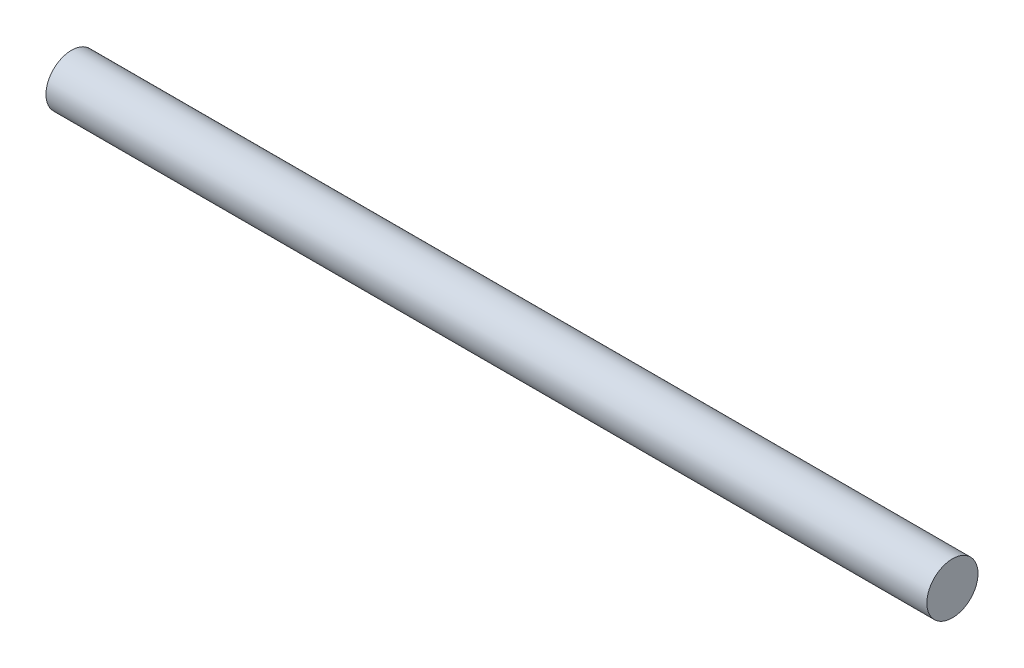
SolidWorks part; units mm, degrees
ref_plane "Plan de face" through (0, 0, 0) normal (0, 0, 1) x (1, 0, 0)
ref_plane "Plan de dessus" through (0, 0, 0) normal (0, 1, 0) x (1, 0, 0)
ref_plane "Plan de droite" through (0, 0, 0) normal (1, 0, 0) x (0, 0, -1)
sketch "Esquisse5" plane through (0, 0, 0) normal (1, 0, 0) x (0, 0, -1)
  circle A0 centre (0, 0) radius 18
extrude "Boss.-Extru.3" add sketch "Esquisse5" along normal blind 620
ref_plane "Plan2" through (10, 0, 0) normal (-1, 0, 0) x (0, 0, 1)
ref_plane "Plan4" through (610, 0, 0) normal (-1, 0, 0) x (0, 0, 1)
sketch "Esquisse6" plane through (10, 0, 0) normal (-1, 0, 0) x (0, 0, 1)
  circle A0 centre (0, 0) radius 18
sketch "Esquisse7" plane through (610, 0, 0) normal (-1, 0, 0) x (0, 0, 1)
  circle A0 centre (0, 0) radius 18
ref_plane "Plan31" through (590, 0, 0) normal (-1, 0, 0) x (0, 0, 1)
sketch "Esquisse32" plane through (590, 0, 0) normal (-1, 0, 0) x (0, 0, 1)
  circle A0 centre (0, 0) radius 18
ref_plane "Plan50" through (530, 0, 0) normal (-1, 0, 0) x (0, 0, 1)
ref_plane "Plan51" through (510, 0, 0) normal (-1, 0, 0) x (0, 0, 1)
ref_plane "Plan52" through (450, 0, 0) normal (-1, 0, 0) x (0, 0, 1)
ref_plane "Plan53" through (430, 0, 0) normal (-1, 0, 0) x (0, 0, 1)
ref_plane "Plan54" through (370, 0, 0) normal (-1, 0, 0) x (0, 0, 1)
ref_plane "Plan55" through (250, 0, 0) normal (-1, 0, 0) x (0, 0, 1)
ref_plane "Plan56" through (190, 0, 0) normal (-1, 0, 0) x (0, 0, 1)
ref_plane "Plan57" through (170, 0, 0) normal (-1, 0, 0) x (0, 0, 1)
ref_plane "Plan58" through (110, 0, 0) normal (-1, 0, 0) x (0, 0, 1)
ref_plane "Plan59" through (90, 0, 0) normal (-1, 0, 0) x (0, 0, 1)
ref_plane "Plan60" through (30, 0, 0) normal (-1, 0, 0) x (0, 0, 1)
sketch "Esquisse53" plane through (530, 0, 0) normal (-1, 0, 0) x (0, 0, 1)
  circle A0 centre (0, 0) radius 18
sketch "Esquisse54" plane through (510, 0, 0) normal (-1, 0, 0) x (0, 0, 1)
  circle A0 centre (0, 0) radius 18
sketch "Esquisse55" plane through (450, 0, 0) normal (-1, 0, 0) x (0, 0, 1)
  circle A0 centre (0, 0) radius 18
sketch "Esquisse56" plane through (430, 0, 0) normal (-1, 0, 0) x (0, 0, 1)
  circle A0 centre (0, 0) radius 18
sketch "Esquisse57" plane through (370, 0, 0) normal (-1, 0, 0) x (0, 0, 1)
  circle A0 centre (0, 0) radius 18
sketch "Esquisse58" plane through (250, 0, 0) normal (-1, 0, 0) x (0, 0, 1)
  circle A0 centre (0, 0) radius 18
sketch "Esquisse59" plane through (190, 0, 0) normal (-1, 0, 0) x (0, 0, 1)
  circle A0 centre (0, 0) radius 18
sketch "Esquisse60" plane through (170, 0, 0) normal (-1, 0, 0) x (0, 0, 1)
  circle A0 centre (0, 0) radius 18
sketch "Esquisse61" plane through (30, 0, 0) normal (-1, 0, 0) x (0, 0, 1)
  circle A0 centre (0, 0) radius 18
sketch "Esquisse62" plane through (90, 0, 0) normal (-1, 0, 0) x (0, 0, 1)
  circle A0 centre (0, 0) radius 18
sketch "Esquisse63" plane through (110, 0, 0) normal (-1, 0, 0) x (0, 0, 1)
  circle A0 centre (0, 0) radius 18
